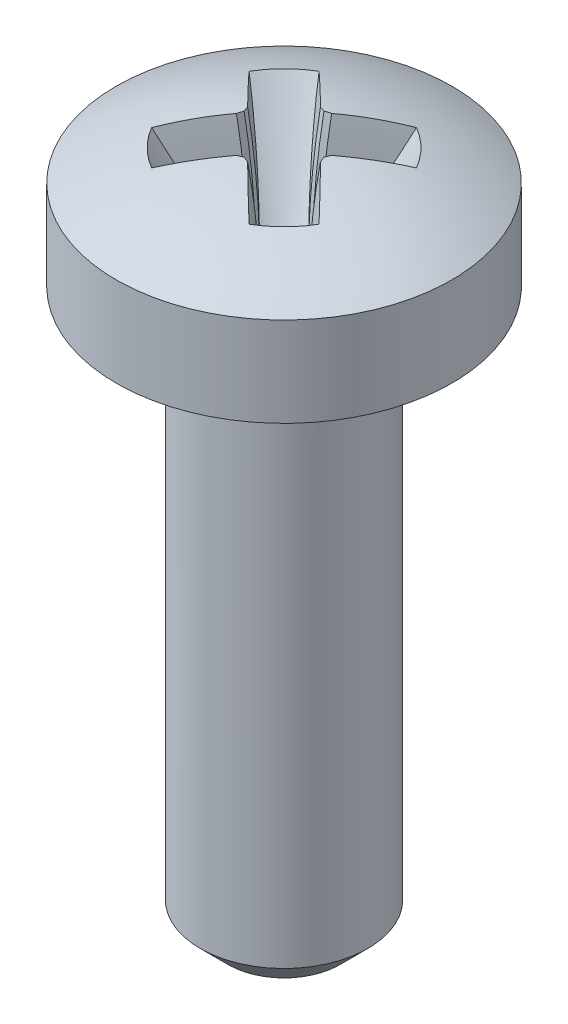
SolidWorks part; units mm, degrees
material "Acier non allié"
ref_plane "Plan de face" through (0, 0, 0) normal (0, 0, 1) x (1, 0, 0)
ref_plane "Plan de dessus" through (0, 0, 0) normal (0, 1, 0) x (1, 0, 0)
ref_plane "Plan de droite" through (0, 0, 0) normal (1, 0, 0) x (0, 0, -1)
sketch "Esquisse1" plane through (0, 0, 0) normal (0, 0, 1) x (1, 0, 0)
  line L0 (0, 0) -> (-1, 0)
  line L1 (-1.5, 0.5) -> (-1.5, 10)
  line L2 (-1.5, 10) -> (-3, 10)
  line L3 (-3, 10) -> (-3, 11.6)
  line L4 (0, 0) -> (0, -0.8642) construction
  line L5 (0, 12.4) -> (0, 0)
  line L6 (-1, 0) -> (-1.5, 0.5)
  line L7 (0, 0) -> (0, 12.4) construction
  arc A1 (0, 12.4) -> (-3, 11.6) centre (0, 6.375) ccw
  point P1 (-1.5, 0)
  dimension "D1" = 0.8
  dimension "D3" = 0.5
  dimension "D2" = 0.5
revolve "Révolution1" add sketch "Esquisse1" angle 360 about L5
sketch "Esquisse3" plane through (0, 0, 0) normal (0, 0, 1) x (1, 0, 0)
  line L1 (-1.5, 9.5) -> (1.5, 9.5)
  line L5 (0, 12.4) -> (0, 0) construction
  point P4 (0, 9.5)
split line "Ligne de séparation16"
sketch "Esquisse4" plane through (0, 0, 0) normal (0, 0, 1) x (1, 0, 0)
  line L0 (0, 20.1) -> (-3, 20.1)
  line L1 (0, 12.4) -> (0, 0) construction
  line L2 (-3, 14.3435) -> (-0.55, 10.1)
  line L3 (-0.55, 10.1) -> (0, 10.1)
  line L4 (0, 9.5) -> (0, 10) construction
  line L5 (0, 10.1) -> (0, 20.1)
  line L6 (-3, 14.3435) -> (-3, 20.1)
  dimension "D1" = 3
  dimension "D2" = 120
  dimension "D3" = 10
revolve "Révolution2" add sketch "Esquisse4" angle 360 about L5
sketch "Esquisse5" plane through (0, 10.1, 0) normal (0, -1, 0) x (1, 0, 0)
  line L0 (-12.5, 12.0636) -> (-0.5364, 0.1)
  line L1 (-0.5364, 0.1) -> (-0.5, 0)
  line L2 (-0.5, 0) -> (-0.5364, -0.1)
  line L3 (-0.5364, -0.1) -> (-12.5, -12.0636)
  line L4 (-12.5, -12.0636) -> (-12.5, 12.0636)
  line L5 (-0.5, 0) -> (0, 0) construction
  dimension "D1" = 12
  dimension "D2" = 140
  dimension "D3" = 90
revolve "Enlèvement de matière-Révolution2" cut sketch "Esquisse5" angle 360 about L4
pattern_circular "Répétition circulaire1" count 4 over 360 about axis through (0, 10.1, 0) along (0, 1, 0) of "Enlèvement de matière-Révolution2"
combine bodies "Combiner1" operation type subtract main body 101 bodies to subtract 108
equation "\"D1@Esquisse1\" = \"F\"/3"
equation "\"D2@Esquisse1\" = \"D\"/6"
equation "\"D3@Esquisse1\" = \"D\"/6"
